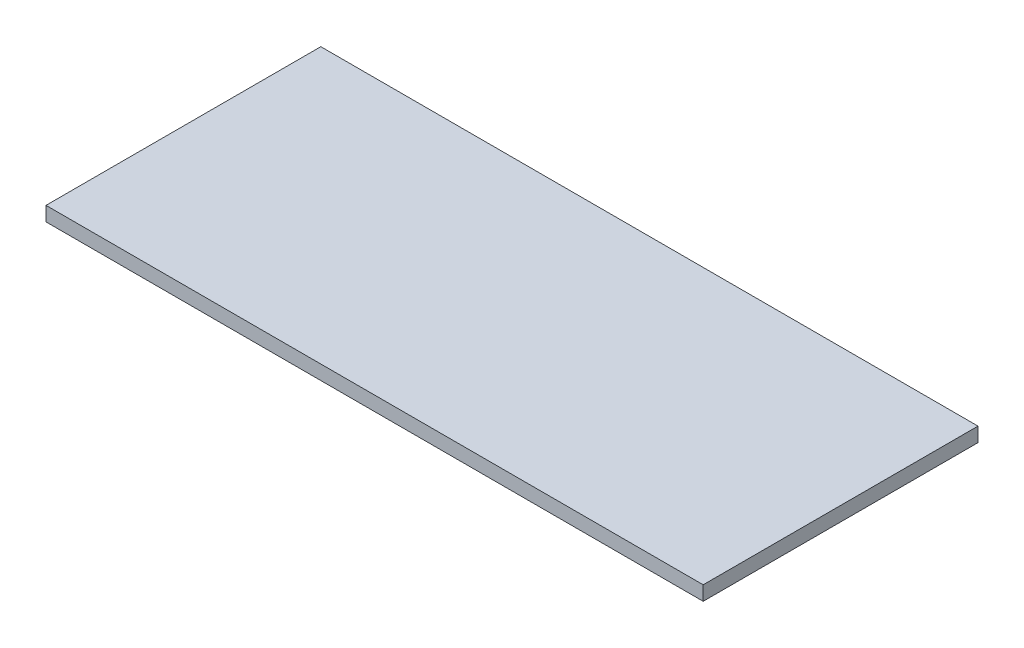
SolidWorks part; units mm, degrees
material "Oak"
ref_plane "Front Plane" through (0, 0, 0) normal (0, 0, 1) x (1, 0, 0)
ref_plane "Top Plane" through (0, 0, 0) normal (0, 1, 0) x (1, 0, 0)
ref_plane "Right Plane" through (0, 0, 0) normal (1, 0, 0) x (0, 0, -1)
sketch "Sketch1" plane through (0, 0, 0) normal (0, 1, 0) x (1, 0, 0)
  line L1 (-436.5625, -182.5625) -> (436.5625, -182.5625)
  line L2 (-436.5625, -182.5625) -> (-436.5625, 182.5625)
  line L3 (-436.5625, 182.5625) -> (436.5625, 182.5625)
  line L4 (436.5625, -182.5625) -> (436.5625, 182.5625)
  line L5 (-436.5625, -182.5625) -> (436.5625, 182.5625) construction
  line L6 (-436.5625, 182.5625) -> (436.5625, -182.5625) construction
  point P0 (0, 0)
  dimension "D1" = 873.125
  dimension "D2" = 365.125
extrude "Boss-Extrude1" add sketch "Sketch1" along normal blind 19.05
